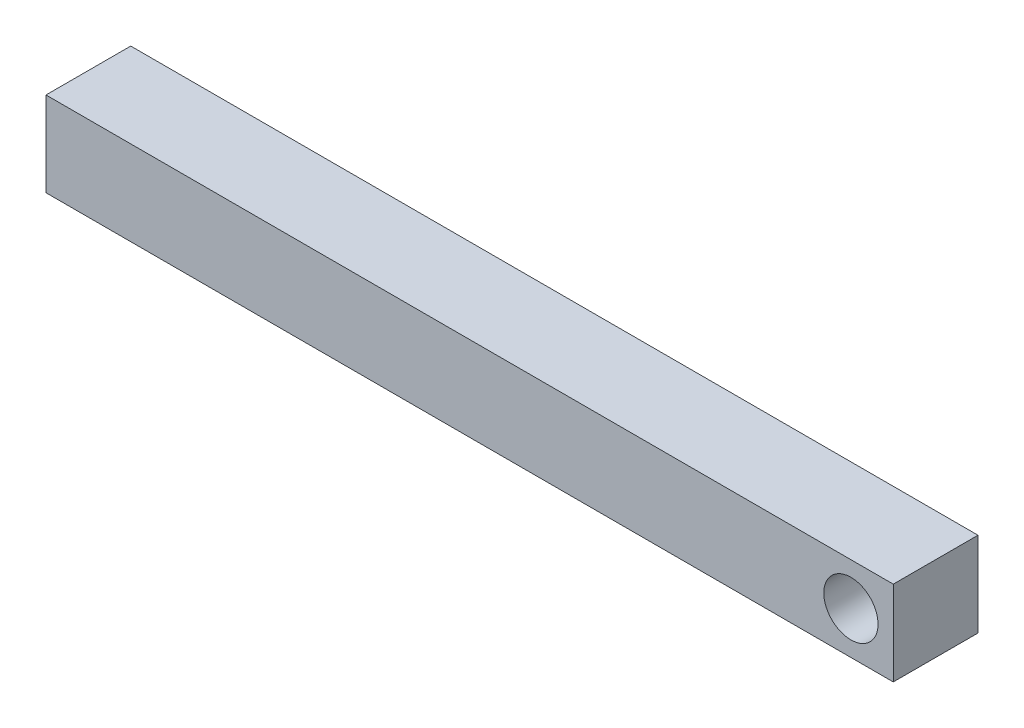
SolidWorks part; units mm, degrees
material "Beech"
ref_plane "Front Plane" through (0, 0, 0) normal (0, 0, 1) x (1, 0, 0)
ref_plane "Top Plane" through (0, 0, 0) normal (0, 1, 0) x (1, 0, 0)
ref_plane "Right Plane" through (0, 0, 0) normal (1, 0, 0) x (0, 0, -1)
sketch "Sketch1" plane through (0, 0, 0) normal (0, 1, 0) x (1, 0, 0)
  line L1 (0, 0) -> (250, 0)
  line L2 (0, 0) -> (0, 25)
  line L3 (0, 25) -> (250, 25)
  line L4 (250, 0) -> (250, 25)
  dimension "D1" = 250
  dimension "D2" = 25
extrude "Boss-Extrude1" add sketch "Sketch1" along normal blind 25
sketch "Sketch2" plane through (0, 0, 0) normal (0, 0, 1) x (1, 0, 0)
  line L0 (0, 0) -> (250, 0) construction
  circle A0 centre (237.5, 12.5) radius 8
  dimension "D3" = 16
  dimension "D1" = 12.5
  dimension "D2" = 12.5
extrude "Cut-Extrude1" cut sketch "Sketch2" against normal through all
